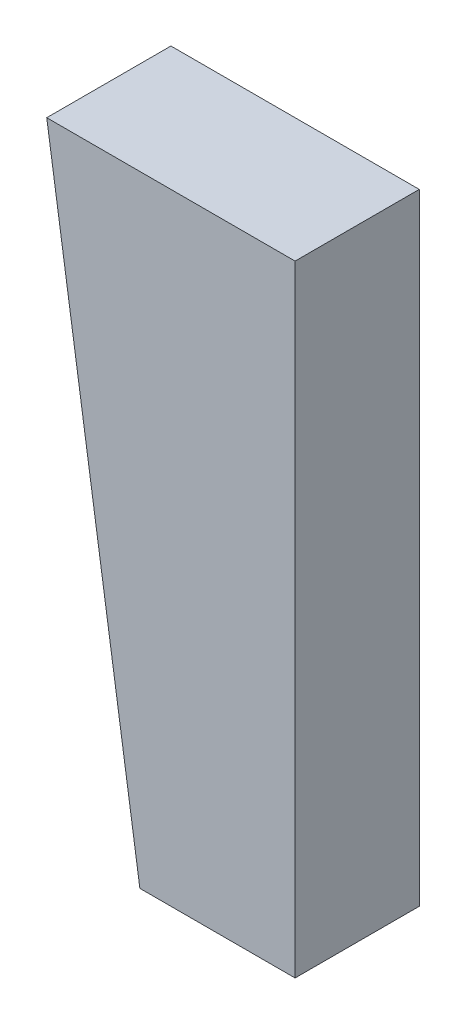
SolidWorks part; units mm, degrees
material "Oak"
ref_plane "Front Plane" through (0, 0, 0) normal (0, 0, 1) x (1, 0, 0)
ref_plane "Top Plane" through (0, 0, 0) normal (0, 1, 0) x (1, 0, 0)
ref_plane "Right Plane" through (0, 0, 0) normal (1, 0, 0) x (0, 0, -1)
sketch "Sketch1" plane through (0, 0, 0) normal (0, 0, 1) x (1, 0, 0)
  line L0 (0, 0) -> (-5, 0)
  line L1 (-5, 0) -> (-8, 20)
  line L2 (-8, 20) -> (0, 20)
  line L3 (0, 20) -> (0, 0)
  dimension "D1" = 8
  dimension "D2" = 5
  dimension "D3" = 20
extrude "Boss-Extrude1" add sketch "Sketch1" along normal blind 4
